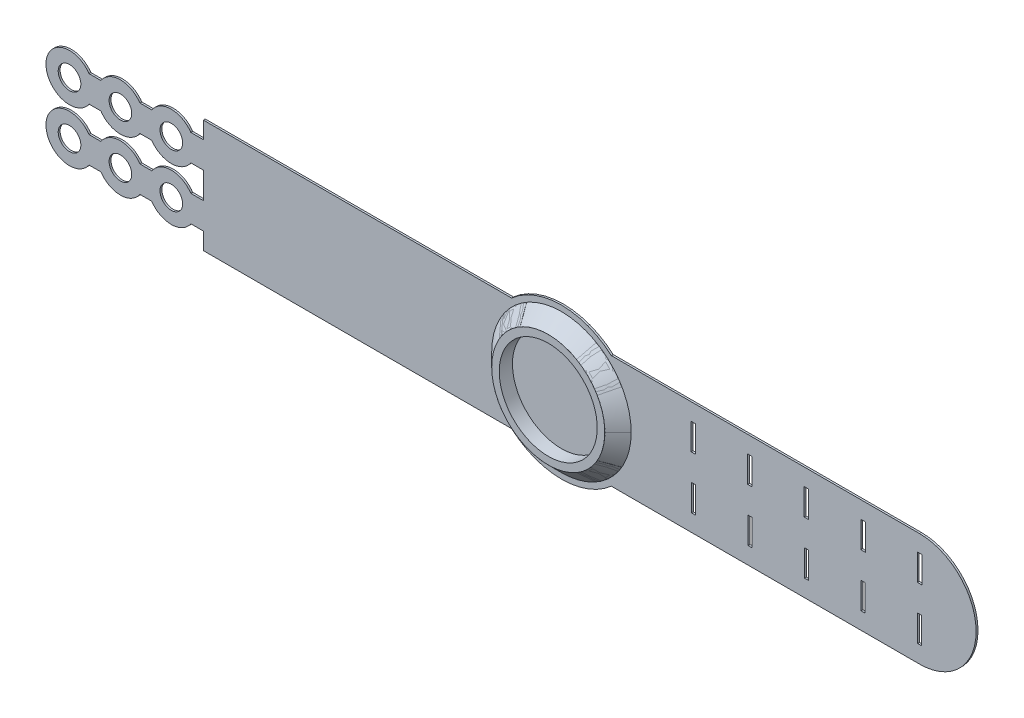
SolidWorks part; units mm, degrees
ref_plane "Спереди" through (0, 0, 0) normal (0, 0, 1) x (1, 0, 0)
ref_plane "Сверху" through (0, 0, 0) normal (0, 1, 0) x (1, 0, 0)
ref_plane "Справа" through (0, 0, 0) normal (1, 0, 0) x (0, 0, -1)
sketch "Эскиз1" plane through (0, 0, 0) normal (0, 0, 1) x (1, 0, 0)
  line L0 (13.2288, 15) -> (95, 15)
  line L1 (-95, 15) -> (-13.2288, 15)
  line L3 (-95, -15) -> (-13.2288, -15)
  line L5 (-95, 15) -> (95, -15) construction
  line L6 (-95, -15) -> (95, 15) construction
  line L7 (13.2288, -15) -> (95, -15)
  line L8 (-95, 15) -> (-95, -15)
  line L9 (80.6, 10.5) -> (80.6, 3.5)
  line L10 (-98.3219, 10.5) -> (-95, 10.5)
  line L12 (-98.3219, 3.5) -> (-95, 3.5)
  line L13 (-95, 10.5) -> (-95, 3.5)
  line L14 (-99.9506, 11.201) -> (-95, 3.5) construction
  line L15 (-99.0084, 4.2647) -> (-95, 10.5) construction
  line L16 (-98.3219, -3.5) -> (-95, -3.5)
  line L18 (-98.3219, -10.5) -> (-95, -10.5)
  line L19 (-95, -3.5) -> (-95, -10.5)
  line L20 (-99.0084, -4.2647) -> (-95, -10.5) construction
  line L21 (-99.9506, -11.201) -> (-95, -3.5) construction
  line L22 (95.6, 10.5) -> (94.4, 10.5)
  line L23 (95.6, 10.5) -> (95.6, 3.5)
  line L24 (95.6, 3.5) -> (94.4, 3.5)
  line L25 (94.4, 10.5) -> (94.4, 3.5)
  line L26 (95.6, 10.5) -> (94.4, 3.5) construction
  line L27 (95.6, 3.5) -> (94.4, 10.5) construction
  line L28 (95.5, -3.5) -> (94.5, -3.5)
  line L29 (95.5, -3.5) -> (95.5, -10.5)
  line L30 (95.5, -10.5) -> (94.5, -10.5)
  line L31 (94.5, -3.5) -> (94.5, -10.5)
  line L32 (95.5, -3.5) -> (94.5, -10.5) construction
  line L33 (95.5, -10.5) -> (94.5, -3.5) construction
  line L34 (80.6, 10.5) -> (79.4, 10.5)
  line L35 (79.4, 10.5) -> (79.4, 3.5)
  line L36 (80.6, 3.5) -> (79.4, 3.5)
  line L37 (80.5, -3.5) -> (79.5, -3.5)
  line L38 (80.5, -3.5) -> (80.5, -10.5)
  line L39 (79.5, -3.5) -> (79.5, -10.5)
  line L40 (80.5, -10.5) -> (79.5, -10.5)
  line L41 (65.6, 10.5) -> (65.6, 3.5)
  line L42 (65.6, 10.5) -> (64.4, 10.5)
  line L43 (64.4, 10.5) -> (64.4, 3.5)
  line L44 (65.6, 3.5) -> (64.4, 3.5)
  line L45 (65.5, -3.5) -> (64.5, -3.5)
  line L46 (65.5, -3.5) -> (65.5, -10.5)
  line L47 (64.5, -3.5) -> (64.5, -10.5)
  line L48 (65.5, -10.5) -> (64.5, -10.5)
  line L49 (50.6, 10.5) -> (50.6, 3.5)
  line L50 (50.6, 10.5) -> (49.4, 10.5)
  line L51 (49.4, 10.5) -> (49.4, 3.5)
  line L52 (50.6, 3.5) -> (49.4, 3.5)
  line L53 (50.5, -3.5) -> (49.5, -3.5)
  line L54 (50.5, -3.5) -> (50.5, -10.5)
  line L55 (49.5, -3.5) -> (49.5, -10.5)
  line L56 (50.5, -10.5) -> (49.5, -10.5)
  line L57 (34.5, -3.5) -> (34.5, -10.5)
  line L58 (35.5, -3.5) -> (35.5, -10.5)
  line L59 (35.5, -10.5) -> (34.5, -10.5)
  line L60 (35.5, -3.5) -> (34.5, -3.5)
  line L61 (35.6, 3.5) -> (34.4, 3.5)
  line L62 (35.6, 10.5) -> (35.6, 3.5)
  line L63 (34.4, 10.5) -> (34.4, 3.5)
  line L64 (35.6, 10.5) -> (34.4, 10.5)
  line L73 (20.5, -3.5) -> (20.5, -10.5)
  line L74 (20.5, -10.5) -> (19.5, -10.5)
  line L75 (20.5, -3.5) -> (19.5, -3.5)
  line L76 (19.4, 10.5) -> (19.4, 3.5)
  line L77 (20.6, 10.5) -> (20.6, 3.5)
  line L78 (20.6, 3.5) -> (19.4, 3.5)
  line L79 (20.6, 10.5) -> (19.4, 10.5)
  line L80 (19.5, -3.5) -> (19.5, -10.5)
  line L81 (-111.8219, 10.5) -> (-108.5, 10.5)
  line L82 (-111.8219, 3.5) -> (-108.5, 3.5)
  line L83 (-111.8219, -3.5) -> (-108.5, -3.5)
  line L84 (-111.8219, -10.5) -> (-108.5, -10.5)
  line L85 (-125.3219, 10.5) -> (-122, 10.5)
  line L86 (-125.3219, 3.5) -> (-122, 3.5)
  line L87 (-125.3219, -3.5) -> (-122, -3.5)
  line L88 (-125.3219, -10.5) -> (-122, -10.5)
  arc A0 (13.2288, 15) -> (-13.2288, 15) centre (0, 0) ccw
  arc A1 (95, -15) -> (95, 15) centre (95, 0) ccw
  arc A2 (-13.2288, -15) -> (13.2288, -15) centre (0, 0) ccw
  arc A3 (-98.3219, 10.5) -> (-98.3219, 3.5) centre (-103.5, 7) ccw
  arc A4 (-98.3219, -3.5) -> (-98.3219, -10.5) centre (-103.5, -7) ccw
  circle A5 centre (-103.5, 7) radius 3
  circle A6 centre (-103.5, -7) radius 3
  arc A7 (-111.8219, 10.5) -> (-111.8219, 3.5) centre (-117, 7) ccw
  circle A8 centre (-117, 7) radius 3
  arc A9 (-111.8219, -3.5) -> (-111.8219, -10.5) centre (-117, -7) ccw
  circle A10 centre (-117, -7) radius 3
  arc A11 (-125.3219, 10.5) -> (-125.3219, 3.5) centre (-130.5, 7) ccw
  circle A12 centre (-130.5, 7) radius 3
  arc A13 (-125.3219, -3.5) -> (-125.3219, -10.5) centre (-130.5, -7) ccw
  circle A14 centre (-130.5, -7) radius 3
  point P0 (0, 0)
  point P11 (-97.25, 7)
  point P17 (-97.25, -7)
  point P23 (-96.661, 3.5)
  point P26 (-96.661, -3.5)
  point P32 (95, 7)
  point P37 (95, -7)
  dimension "D3" = 40
  dimension "D4" = 20
  dimension "D5" = 0
  dimension "D6" = 5
  dimension "D12" = 12.5
  dimension "D13" = 12.5
  dimension "D16" = 6
  dimension "D17" = 6
  dimension "D18" = 8.5
  dimension "D21" = 8.5
  dimension "D1" = 190
  dimension "D2" = 30
  dimension "D7" = 5
  dimension "D8" = 8
  dimension "D9" = 8
  dimension "D10" = 7
  dimension "D11" = 7
  dimension "D14" = 8
  dimension "D15" = 8
  dimension "D19" = 4.5
  dimension "D20" = 11.5
  dimension "D22" = 4.5
  dimension "D23" = 18.5
  dimension "D24" = 8
  dimension "D25" = 8
  dimension "D26" = 7
  dimension "D27" = 7
  dimension "D28" = 1.2
  dimension "D29" = 1
  dimension "D31" = 14.4
  dimension "D33" = 14
  dimension "D34" = 3
  dimension "D30" = 4
  dimension "D32" = 3
extrude "Бобышка-Вытянуть2" add sketch "Эскиз1" along normal blind 0.5
sketch "Эскиз3" plane through (0, 0, 0) normal (0, 0, -1) x (-1, 0, 0)
  circle A0 centre (0, 0) radius 13
  circle A1 centre (0, 0) radius 15
  dimension "D1" = 26
  dimension "D2" = 30
extrude "Бобышка-Вытянуть3" add sketch "Эскиз3" against normal blind 4
sketch3d "Трехмерный эскиз1"
  line L0 (15, 0, 0.5) -> (18.5, 0, 0.5)
  line L1 (15, 0, 4) -> (18.5, 0, 0.5)
  line L2 (15, 0, 4) -> (15, 0, 0.5)
  circle A0 centre (0, 0, 0.5) radius 15 construction
  circle A1 centre (0, 0, 4) radius 15 construction
  point P4 (0, 0, 15.5)
  point P6 (0, 0, 0)
  point P9 (0, 0, -11)
  point P10 (0, 0, 0)
  dimension "D1" = 45
sketch "Эскиз7" plane through (0, 0, 0) normal (0, 0, -1) x (-1, 0, 0)
surface "Поверхность-По траектории1"
sketch "Эскиз8" plane through (0, 0, 0.5) normal (0, 0, 1) x (1, 0, 0)
  line L0 (0, 0) -> (27.3928, 15.8152) construction
  line L1 (0, 0) -> (38.8687, 0)
  line L2 (0, 0) -> (11.1834, 19.3702) construction
  line L3 (7.5, 12.9904) -> (9.2309, 15.9884)
  line L4 (12.9904, 7.5) -> (15.9884, 9.2309)
  line L5 (7.5, -12.9904) -> (9.2309, -15.9884)
  line L6 (12.9904, -7.5) -> (15.9884, -9.2309)
  line L7 (-12.9904, -7.5) -> (-15.9884, -9.2309)
  line L8 (-7.5, -12.9904) -> (-9.2309, -15.9884)
  line L9 (-7.5, 12.9904) -> (-9.2309, 15.9884)
  line L10 (-12.9904, 7.5) -> (-15.9884, 9.2309)
  arc A0 (12.9904, 7.5) -> (7.5, 12.9904) centre (0, 0) ccw
  arc A1 (15.9884, 9.2309) -> (9.2309, 15.9884) centre (0, 0) ccw
  arc A2 (9.2309, -15.9884) -> (15.9884, -9.2309) centre (0, 0) ccw
  arc A3 (7.5, -12.9904) -> (12.9904, -7.5) centre (0, 0) ccw
  arc A4 (-15.9884, -9.2309) -> (-9.2309, -15.9884) centre (0, 0) ccw
  arc A5 (-12.9904, -7.5) -> (-7.5, -12.9904) centre (0, 0) ccw
  arc A6 (-9.2309, 15.9884) -> (-15.9884, 9.2309) centre (0, 0) ccw
  arc A7 (-7.5, 12.9904) -> (-12.9904, 7.5) centre (0, 0) ccw
  circle A8 centre (0, 0) radius 15 construction
  point P9 (7.5, 12.9904)
  point P24 (0, 0)
  dimension "D1" = 30
  dimension "D2" = 30
  dimension "D3" = 4
extrude "Бобышка-Вытянуть4" add sketch "Эскиз8" along normal blind 3.5 separate body contours L4 A1 L3 A0 | A3 L5 A2 L6 | A5 L7 A4 L8 | A7 L9 A6 L10
sketch3d "Трехмерный эскиз2"
  line L2 (17.6563, 5.523, 0.5) -> (14.314, 4.4842, 4)
  line L3 (14.314, 4.4842, 4) -> (17.6542, 5.5297, 4)
  line L4 (17.6542, 5.5297, 4) -> (17.6563, 5.523, 0.5)
  circle A0 centre (0, 0, 4) radius 15 construction
  point P5 (0, 0, -11)
  dimension "D1" = 90
sweep "Вырез-По траектории1" cut profiles "Трехмерный эскиз2" path edge at (-13, 0, 4)
